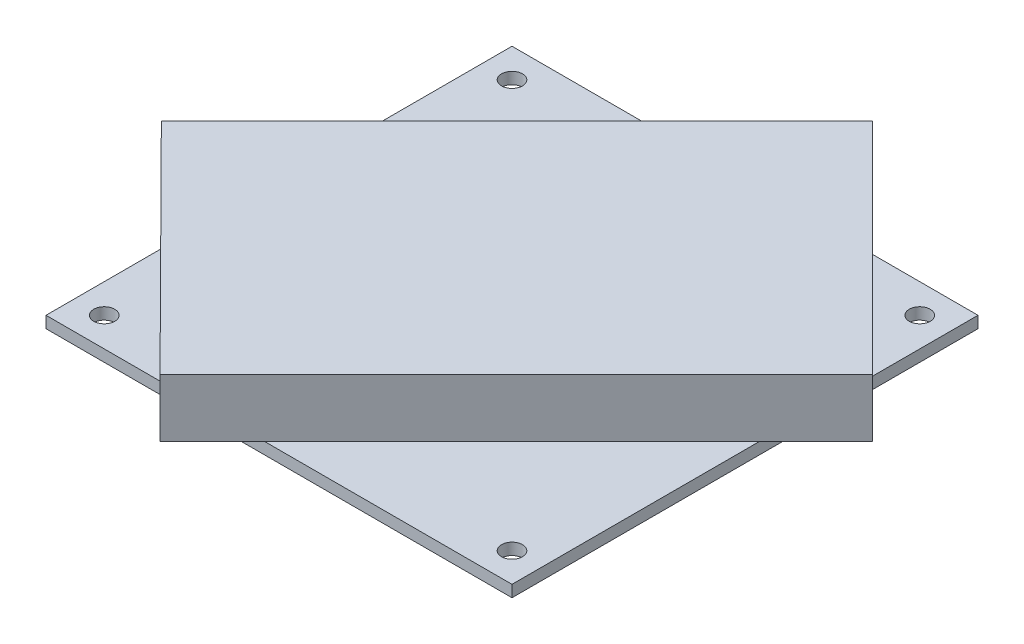
SolidWorks part; units mm, degrees
ref_plane "Front Plane" through (0, 0, 0) normal (0, 0, 1) x (1, 0, 0)
ref_plane "Top Plane" through (0, 0, 0) normal (0, 1, 0) x (1, 0, 0)
ref_plane "Right Plane" through (0, 0, 0) normal (1, 0, 0) x (0, 0, -1)
sketch "Sketch1" plane through (0, 0, 0) normal (0, 1, 0) x (1, 0, 0)
  line L1 (0, 0) -> (80, 0)
  line L2 (0, 0) -> (0, 80)
  line L3 (0, 80) -> (80, 80)
  line L4 (80, 0) -> (80, 80)
  dimension "D1" = 80
  dimension "D2" = 80
extrude "PCB" add sketch "Sketch1" along normal blind 2
sketch "Sketch2" plane through (0, 2, 0) normal (0, 1, 0) x (1, 0, 0)
  line L0 (80, 80) -> (0, 80) construction
  line L1 (0, 80) -> (0, 0) construction
  circle A0 centre (5, 75) radius 1.8
  dimension "D1" = 3.6
  dimension "D2" = 5
  dimension "D3" = 5
extrude "Attachment Holes" cut sketch "Sketch2" against normal through all
pattern_linear "LPattern1" count 2 spacing 70 along (1, 0, 0) count 2 spacing 70 along (0, 0, 1) of "Attachment Holes"
sketch "Sketch3" plane through (0, 2, 0) normal (0, 1, 0) x (1, 0, 0)
  line L1 (0, 0) -> (80, 0) construction
  line L2 (-9, 28.8007) -> (52.0233, 89.824)
  line L3 (-9, 28.8007) -> (28.5765, -9)
  line L4 (28.5765, -9) -> (89.7119, 52.1354)
  line L5 (80, 80) -> (0, 80) construction
  line L6 (52.0233, 89.824) -> (89.7119, 52.1354)
  line L7 (0, 80) -> (0, 0) construction
  line L8 (80, 0) -> (80, 80) construction
  dimension "D1" = 86.3
  dimension "D2" = 53.3
  dimension "D3" = 9
  dimension "D4" = 9
  dimension "D5" = 28.8007
  dimension "D6" = 9.824
  dimension "D7" = 9.7119
  dimension "D8" = 53.2998
extrude "Iduino" add sketch "Sketch3" along normal blind 10
